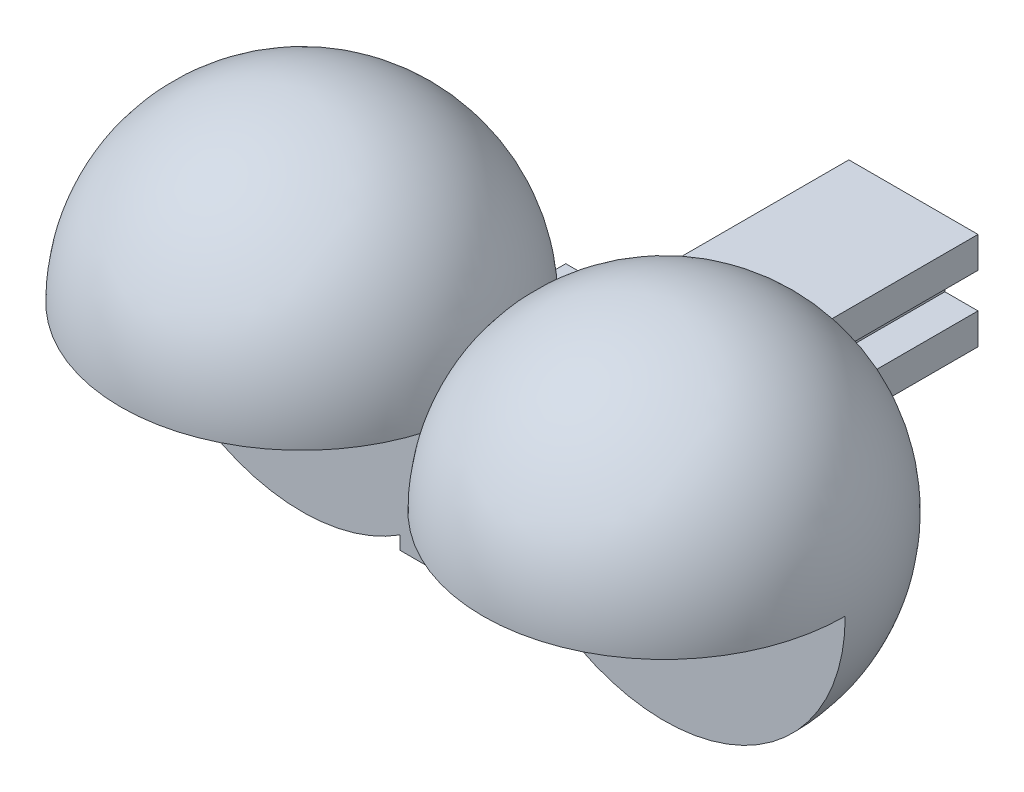
SolidWorks part; units mm, degrees
ref_plane "Front Plane" through (0, 0, 0) normal (0, 0, 1) x (1, 0, 0)
ref_plane "Top Plane" through (0, 0, 0) normal (0, 1, 0) x (1, 0, 0)
ref_plane "Right Plane" through (0, 0, 0) normal (1, 0, 0) x (0, 0, -1)
sketch "Sketch1" plane through (0, 0, 0) normal (0, 0, 1) x (1, 0, 0)
  line L0 (0, 96.3329) -> (0, -96.3329) construction
  line L1 (-189.143, 0) -> (189.143, 0) construction
  line L2 (-54.7, 103.1073) -> (-54.7, -103.1073) construction
  line L3 (54.7, 99.8556) -> (54.7, -99.8556) construction
  line L4 (-54.7, 0) -> (0, 0)
  line L5 (0, 0) -> (54.7, 0)
  arc A0 (0, 0) -> (-54.7, 0) centre (-27.35, 0) ccw
  arc A1 (0, 0) -> (54.7, 0) centre (27.35, 0) cw
  point P4 (0, 0)
  point P8 (0, 0)
  point P11 (-54.7, 0)
  point P14 (54.7, 0)
  dimension "D3" = 27.35
  dimension "D1" = 54.7
  dimension "D2" = 109.4
revolve "Revolve1" add sketch "Sketch1" angle 360 about L5
sketch "Sketch5" plane through (0, 0, 0) normal (0, 1, 0) x (1, 0, 0)
  line L0 (-86.0609, 0) -> (86.0609, 0) construction
  line L2 (-58.0027, 0) -> (73.8002, 0)
  line L3 (-58.0027, 0) -> (-58.0027, -32.3613)
  line L4 (-58.0027, -32.3613) -> (73.8002, -32.3613)
  line L5 (73.8002, 0) -> (73.8002, -32.3613)
  point P4 (0, 0)
extrude "Cut-Extrude2" cut sketch "Sketch5" against normal blind 27.35
sketch "Sketch6" plane through (0, 0, 0) normal (0, 0, 1) x (1, 0, 0)
  line L0 (-88.183, 0) -> (88.183, 0) construction
  line L3 (0, 41.0853) -> (0, -41.0853) construction
  line L4 (-54.7, 0) -> (-54.7, -38.9632) construction
  line L5 (54.7, 0) -> (54.7, -38.9632) construction
  line L6 (-27.35, 0) -> (-27.35, -33.0191)
  line L7 (-42.35, 0) -> (-12.35, 0)
  line L8 (42.35, 0) -> (12.35, 0)
  arc A0 (-54.7, 0) -> (0, 0) centre (-27.35, 0) ccw construction
  arc A1 (-12.35, 0) -> (-42.35, 0) centre (-27.35, 0) ccw
  arc A2 (12.35, 0) -> (42.35, 0) centre (27.35, 0) cw
  arc A3 (-12.35, 0) -> (-42.35, 0) centre (-27.35, 0) ccw
  arc A4 (42.35, 0) -> (12.35, 0) centre (27.35, 0) ccw
  point P4 (0, 0)
  point P7 (0, 0)
  dimension "D2" = 15
  dimension "D1" = 27.35
revolve "Revolve2" add sketch "Sketch6" angle 360 about L0
sketch "Sketch7" plane through (0, 0, 0) normal (0, 0, 1) x (1, 0, 0)
  line L0 (95.0291, 0) -> (-95.0291, 0) construction
  line L1 (0, 60.4182) -> (0, -60.4182) construction
  line L3 (12.5, 0) -> (-12.5, 0)
  line L4 (12.5, 0) -> (12.5, -25)
  line L5 (12.5, -25) -> (-12.5, -25)
  line L6 (-12.5, 0) -> (-12.5, -25)
  point P4 (0, 0)
  point P8 (0, 0)
  dimension "D1" = 25
  dimension "D2" = 12.5
  dimension "D3" = 25
extrude "Boss-Extrude1" add sketch "Sketch7" against normal blind 40 contours L4 L3 L6 L5
sketch "Sketch8" plane through (0, 0, 0) normal (0, 0, 1) x (1, 0, 0)
  line L0 (0, 54.0699) -> (0, -54.0699) construction
  line L2 (12.5, -25) -> (-12.5, -25) construction
  line L4 (9.75, -5.0472) -> (-9.75, -5.0472)
  line L10 (12.5, 0) -> (-12.5, 0) construction
  line L11 (-9.75, -5.0472) -> (-9.75, -9.7472)
  line L12 (-9.75, -9.7472) -> (-4.75, -9.7472)
  line L13 (-4.75, -9.7472) -> (-4.75, -15.0472)
  line L14 (-4.75, -15.0472) -> (-9.75, -15.0472)
  line L15 (-9.75, -15.0472) -> (-9.75, -19.7472)
  line L16 (-9.75, -19.7472) -> (9.75, -19.7472)
  line L17 (9.75, -15.0472) -> (9.75, -19.7472)
  line L18 (4.75, -15.0472) -> (9.75, -15.0472)
  line L19 (4.75, -9.7472) -> (4.75, -15.0472)
  line L20 (9.75, -9.7472) -> (4.75, -9.7472)
  line L21 (9.75, -5.0472) -> (9.75, -9.7472)
  line L23 (12.5, 0) -> (-12.5, 0)
  line L24 (12.5, 0) -> (12.5, -25)
  line L25 (12.5, -25) -> (-12.5, -25)
  line L26 (-12.5, 0) -> (-12.5, -25)
  point P4 (0, 0)
  point P15 (0, -19.7472)
  point P21 (0, -25)
  point P23 (0, -5.0472)
  point P26 (0, 0)
  dimension "D1" = 9.75
  dimension "D2" = 4.7
  dimension "D3" = 5.3
  dimension "D4" = 4.7
  dimension "D5" = 5
  dimension "D6" = 5
extrude "Cut-Extrude3" cut sketch "Sketch8" along normal blind 30 from offset 55 contours L11 L12 L13 L14 L15 L16 L17 L18 L19 L20 L21 L4 offset against normal yes
sketch "Sketch9" plane through (0, 0, 0) normal (0, 0, 1) x (1, 0, 0)
  line L0 (9.75, -5.0472) -> (9.75, -9.7472)
  line L1 (9.75, -9.7472) -> (4.75, -9.7472)
  line L2 (4.75, -9.7472) -> (4.75, -15.0472)
  line L3 (4.75, -15.0472) -> (9.75, -15.0472)
  line L4 (9.75, -15.0472) -> (9.75, -19.7472)
  line L5 (9.75, -19.7472) -> (-9.75, -19.7472)
  line L6 (-9.75, -19.7472) -> (-9.75, -15.0472)
  line L7 (-9.75, -15.0472) -> (-4.75, -15.0472)
  line L8 (-4.75, -15.0472) -> (-4.75, -9.7472)
  line L9 (-4.75, -9.7472) -> (-9.75, -9.7472)
  line L10 (-9.75, -9.7472) -> (-9.75, -5.0472)
  line L11 (-9.75, -5.0472) -> (9.75, -5.0472)
extrude "Boss-Extrude3" add sketch "Sketch9" against normal blind 25 from offset 40 contours L11 L0 L1 L2 L3 L4 L5 L6 L7 L8 L9 L10 offset against normal yes
sketch "Sketch10" plane through (0, 0, 0) normal (0, 0, 1) x (1, 0, 0)
  line L0 (0, 45.8009) -> (0, -45.8009) construction
  line L4 (-9.5, -9.4501) -> (9.5, -9.4501)
  line L5 (-9.5, -9.4501) -> (-9.5, -22)
  line L6 (-9.5, -22) -> (9.5, -22)
  line L7 (9.5, -9.4501) -> (9.5, -22)
  line L8 (-9.5, -9.4501) -> (9.5, -22) construction
  line L9 (-9.5, -22) -> (9.5, -9.4501) construction
  line L10 (12.5, -25) -> (-12.5, -25) construction
  line L11 (-12.5, -22.9674) -> (-12.5, -25) construction
  line L12 (-23.9984, -15.725) -> (23.9984, -15.725) construction
  line L13 (7, -18.725) -> (1, -18.725)
  line L14 (-7, -12.725) -> (-1, -12.725)
  line L15 (-7, -12.725) -> (-7, -18.725)
  line L16 (-7, -18.725) -> (-1, -18.725)
  line L17 (-1, -12.725) -> (-1, -18.725)
  line L18 (-7, -12.725) -> (-1, -18.725) construction
  line L19 (-7, -18.725) -> (-1, -12.725) construction
  line L20 (1, -12.725) -> (1, -18.725)
  line L21 (7, -12.725) -> (1, -12.725)
  line L22 (7, -12.725) -> (7, -18.725)
  point P0 (0, -15.725)
  point P4 (0, 0)
  point P7 (0, -15.725)
  point P14 (-4, -15.725)
  point P17 (0, -15.725)
  dimension "D1" = 3
  dimension "D2" = 3
  dimension "D3" = 6
  dimension "D4" = 6
  dimension "D5" = 2.5
extrude "Cut-Extrude4" cut sketch "Sketch10" against normal blind 25 contours L13 L20 L21 L22 | L15 L14 L17 L16
